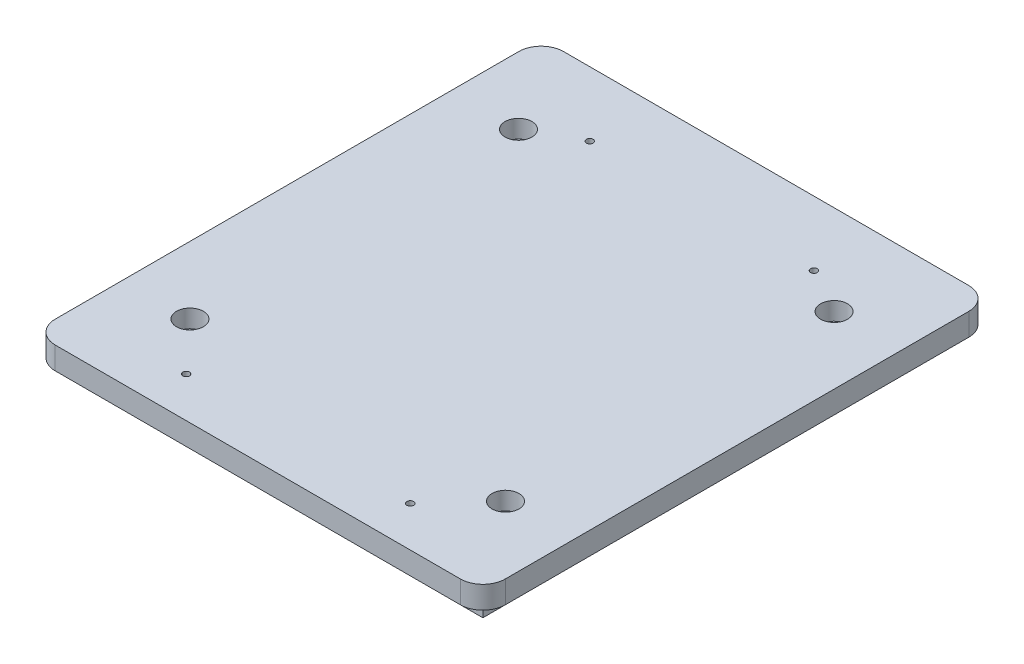
SolidWorks part; units mm, degrees
ref_plane "Front Plane" through (0, 0, 0) normal (0, 0, 1) x (1, 0, 0)
ref_plane "Top Plane" through (0, 0, 0) normal (0, 1, 0) x (1, 0, 0)
ref_plane "Right Plane" through (0, 0, 0) normal (1, 0, 0) x (0, 0, -1)
sketch "Sketch1" plane through (0, 0, 0) normal (0, 1, 0) x (1, 0, 0)
  line L1 (-50.2, -56.7) -> (50.2, -56.7)
  line L2 (-50.2, -56.7) -> (-50.2, 56.7)
  line L3 (-50.2, 56.7) -> (50.2, 56.7)
  line L4 (50.2, -56.7) -> (50.2, 56.7)
  line L5 (-50.2, -56.7) -> (50.2, 56.7) construction
  line L6 (-50.2, 56.7) -> (50.2, -56.7) construction
  point P0 (0, 0)
  dimension "D1" = 100.4
  dimension "D2" = 113.4
extrude "Boss-Extrude1" add sketch "Sketch1" along normal blind 5
sketch "Sketch2" plane through (0, 0, 0) normal (0, -1, 0) x (1, 0, 0)
  line L0 (50.2, 56.7) -> (50.2, -56.7) construction
  line L1 (-45.2, -51.7) -> (45.2, -51.7)
  line L2 (-45.2, -51.7) -> (-45.2, 51.7)
  line L3 (-45.2, 51.7) -> (45.2, 51.7)
  line L4 (45.2, -51.7) -> (45.2, 51.7)
  line L5 (-45.2, -51.7) -> (45.2, 51.7) construction
  line L6 (-45.2, 51.7) -> (45.2, -51.7) construction
  line L8 (-50.2, 56.7) -> (50.2, 56.7) construction
  point P0 (0, 0)
  dimension "D1" = 5
  dimension "D2" = 5
extrude "Boss-Extrude2" add sketch "Sketch2" along normal blind 5
fillet "Fillet1" radius 5 4 edges at (-50.2, 2.5, -56.7) (50.2, 2.5, -56.7) (50.2, 2.5, 56.7) (-50.2, 2.5, 56.7)
sketch "Sketch3" plane through (0, 5, 0) normal (0, 1, 0) x (1, 0, 0)
  line L0 (45.2, 56.7) -> (-45.2, 56.7) construction
  line L1 (-50.2, 51.7) -> (-50.2, -51.7) construction
  circle A0 centre (-35.2, 36.65) radius 1.5
  circle A1 centre (-35.2, -36.65) radius 1.5
  circle A2 centre (35.2, 36.65) radius 1.5
  circle A3 centre (35.2, -36.65) radius 1.5
  dimension "D1" = 73.3
  dimension "D5" = 20.05
  dimension "D2" = 73.3
  dimension "D3" = 70.4
  dimension "D4" = 70.4
  dimension "D6" = 15
extrude "Cut-Extrude1" cut sketch "Sketch3" against normal blind 17
sketch "Sketch4" plane through (0, 5, 0) normal (0, 1, 0) x (1, 0, 0)
  circle A0 centre (-35.2, 36.65) radius 3
  circle A1 centre (-35.2, -36.65) radius 3
  circle A2 centre (35.2, 36.65) radius 3
  circle A3 centre (35.2, -36.65) radius 3
extrude "Cut-Extrude2" cut sketch "Sketch4" against normal blind 4
sketch "Sketch5" plane through (0, 5, 0) normal (0, 1, 0) x (1, 0, 0)
  line L2 (-50.2, 51.7) -> (-50.2, -51.7) construction
  line L3 (50.2, -51.7) -> (50.2, 51.7) construction
  line L4 (-45.2, -56.7) -> (45.2, -56.7) construction
  circle A0 centre (-24.9457, 42.3) radius 0.75
  circle A1 centre (-25, -47.7) radius 0.75
  circle A2 centre (25.0543, 42.3) radius 0.75
  circle A3 centre (25, -47.7) radius 0.75
  dimension "D1" = 50
  dimension "D2" = 50
  dimension "D3" = 90
  dimension "D4" = 90
  dimension "D5" = 9
  dimension "D6" = 9
  dimension "D7" = 25.2543
  dimension "D8" = 25.2
extrude "Cut-Extrude3" cut sketch "Sketch5" against normal blind 19
